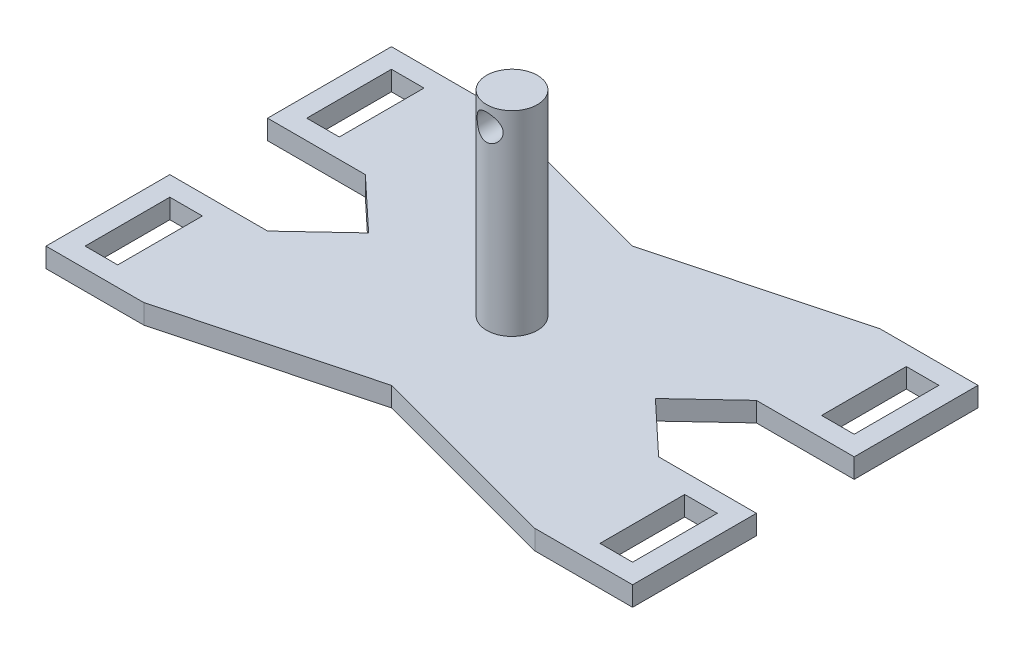
SolidWorks part; units mm, degrees
ref_plane "Alzado" through (0, 0, 0) normal (0, 0, 1) x (1, 0, 0)
ref_plane "Planta" through (0, 0, 0) normal (0, 1, 0) x (1, 0, 0)
ref_plane "Vista lateral" through (0, 0, 0) normal (1, 0, 0) x (0, 0, -1)
sketch "Croquis1" plane through (0, 0, 0) normal (0, 1, 0) x (1, 0, 0)
  line L0 (-45, -26.5) -> (-30, -26.5)
  line L1 (-30, -26.5) -> (30, -26.5) construction
  line L2 (30, -26.5) -> (30, -7.5) construction
  line L3 (-30, 26.5) -> (30, 26.5) construction
  line L4 (30, 7.5) -> (30, 26.5) construction
  line L5 (-30, -26.5) -> (30, 26.5) construction
  line L6 (30, -26.5) -> (-30, 26.5) construction
  line L7 (30, -26.5) -> (45, -26.5)
  line L8 (45, -26.5) -> (45, -7.5)
  line L9 (45, -7.5) -> (30, -7.5)
  line L10 (30, -7.5) -> (30, 7.5) construction
  line L11 (30, 7.5) -> (45, 7.5)
  line L12 (45, 7.5) -> (45, 26.5)
  line L13 (45, 26.5) -> (30, 26.5)
  line L14 (30, -26.5) -> (0, -18.5)
  line L15 (0, -18.5) -> (-30, -26.5)
  line L16 (-30, 26.5) -> (-45, 26.5)
  line L17 (-45, 26.5) -> (-45, 7.5)
  line L18 (-45, 7.5) -> (-30, 7.5)
  line L19 (-30, 7.5) -> (-30, -7.5) construction
  line L20 (-30, -7.5) -> (-45, -7.5)
  line L21 (-45, -7.5) -> (-45, -26.5)
  line L22 (-30, -7.5) -> (-22, 0)
  line L23 (-22, 0) -> (-30, 7.5)
  line L24 (-30, 7.5) -> (-30, 26.5) construction
  line L25 (-30, -26.5) -> (-30, -7.5) construction
  line L26 (-30, 26.5) -> (0, 18.5)
  line L27 (0, 18.5) -> (30, 26.5)
  line L28 (30, 7.5) -> (22, 0)
  line L29 (22, 0) -> (30, -7.5)
  line L30 (42, -10.5) -> (45, -10.5) construction
  line L31 (42, -10.5) -> (37, -10.5)
  line L32 (42, -10.5) -> (42, -23.5)
  line L33 (42, -23.5) -> (37, -23.5)
  line L34 (37, -10.5) -> (37, -23.5)
  line L35 (42, -10.5) -> (42, -7.5) construction
  line L36 (42, -23.5) -> (42, -26.5) construction
  line L37 (-42, 23.5) -> (-42, 26.5) construction
  line L38 (42, 23.5) -> (37, 23.5)
  line L39 (42, 23.5) -> (42, 10.5)
  line L40 (42, 10.5) -> (37, 10.5)
  line L41 (37, 23.5) -> (37, 10.5)
  line L42 (-42, 23.5) -> (-37, 23.5)
  line L43 (-42, 23.5) -> (-42, 10.5)
  line L44 (-42, 10.5) -> (-37, 10.5)
  line L45 (-37, 23.5) -> (-37, 10.5)
  line L46 (-42, -10.5) -> (-37, -10.5)
  line L47 (-42, -10.5) -> (-42, -23.5)
  line L48 (-42, -23.5) -> (-37, -23.5)
  line L49 (-37, -10.5) -> (-37, -23.5)
  line L50 (-42, 23.5) -> (-45, 23.5) construction
  line L51 (-42, -10.5) -> (-45, -10.5) construction
  line L52 (-42, -10.5) -> (-42, -7.5) construction
  line L53 (42, 23.5) -> (42, 26.5) construction
  line L54 (42, 23.5) -> (45, 23.5) construction
  point P0 (0, 0)
  point P1 (0, 0)
  point P48 (42, -17)
  point P49 (42, 17)
  point P50 (39.5, -10.5)
  dimension "D6" = 3
  dimension "D1" = 60
  dimension "D2" = 34
  dimension "D3" = 13
  dimension "D4" = 9.5
  dimension "D5" = 8
  dimension "D7" = 8
  dimension "D8" = 5
extrude "Saliente-Extruir1" add sketch "Croquis1" along normal blind 3
sketch "Croquis9" plane through (0, 3, 0) normal (0, 1, 0) x (1, 0, 0)
  circle A0 centre (0, 0) radius 3.9
  dimension "D1" = 7.8
extrude "Saliente-Extruir2" add sketch "Croquis9" along normal blind 30
sketch "Croquis10" plane through (0, 0, 0) normal (0, 0, 1) x (1, 0, 0)
  line L0 (0, 0) -> (0, 30) construction
  circle A0 centre (0, 30) radius 2
  dimension "D1" = 4
  dimension "D2" = 30
extrude "Cortar-Extruir7" cut sketch "Croquis10" against normal through all and the other way through all
